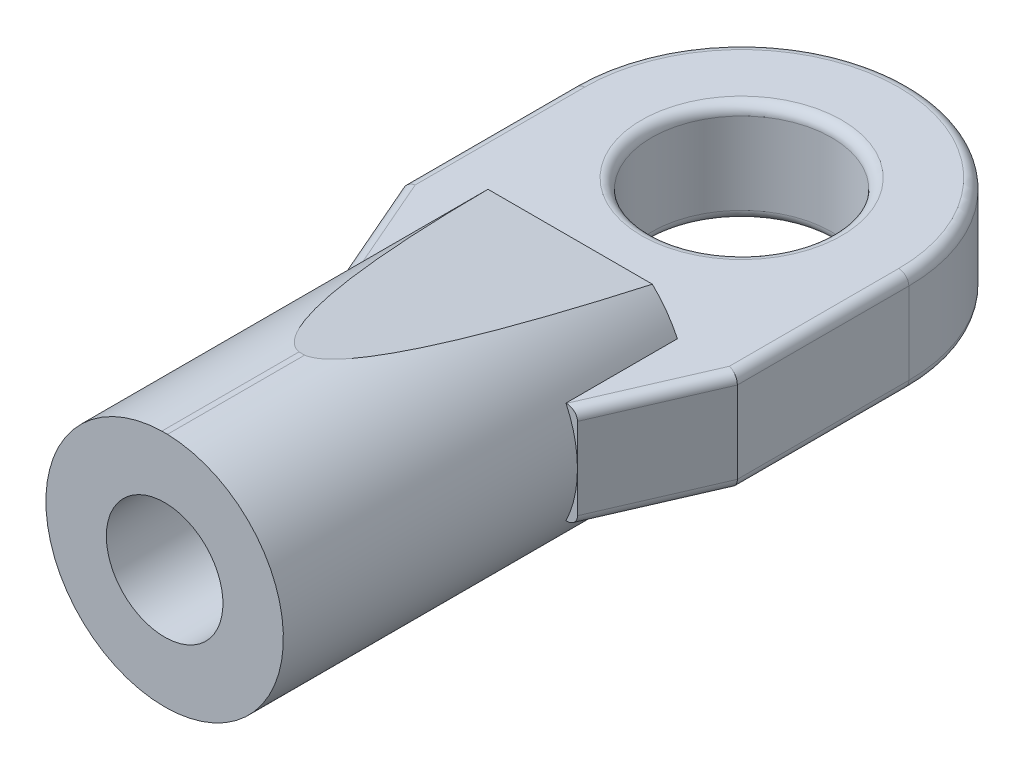
SolidWorks part; units mm, degrees
material "ABS"
ref_plane "Front Plane" through (0, 0, 0) normal (0, 0, 1) x (1, 0, 0)
ref_plane "Top Plane" through (0, 0, 0) normal (0, 1, 0) x (1, 0, 0)
ref_plane "Right Plane" through (0, 0, 0) normal (1, 0, 0) x (0, 0, -1)
sketch "Sketch1" plane through (0, 0, 0) normal (0, 1, 0) x (1, 0, 0)
  line L0 (0, -17.0942) -> (-1.7272, -17.0942)
  line L1 (0, 0) -> (0, -17.0942) construction
  line L2 (-3.5179, -17.0942) -> (-3.5179, -5.08)
  line L3 (-1.7272, -5.6642) -> (0, -5.6642)
  line L4 (-4.953, 0) -> (-4.953, -5.08)
  line L5 (4.953, 0) -> (4.953, -5.08)
  line L6 (-3.5179, -8.382) -> (-4.953, -5.08)
  line L7 (3.5179, -8.382) -> (4.953, -5.08)
  line L8 (-1.7272, -17.0942) -> (-1.7272, -5.6642)
  line L9 (-3.5179, -5.08) -> (0, -5.08)
  line L10 (-3.5179, -17.0942) -> (-1.7272, -17.0942)
  circle A0 centre (0, 0) radius 2.667
  arc A1 (4.953, 0) -> (-4.953, 0) centre (0, 0) ccw
  dimension "D1" = 2.286
  dimension "D7" = 1.7907
  dimension "D2" = 4.953
  dimension "D3" = 5.08
  dimension "D4" = 1.7272
  dimension "D5" = 3.6004
  dimension "D6" = 1.4351
  dimension "D8" = 11.43
  dimension "D9" = 12.0142
  dimension "D10" = 6.5674
revolve "Revolve1" add sketch "Sketch1" angle 360 about L1
sketch "Sketch2" plane through (0, 0, 0) normal (1, 0, 0) x (0, 0, -1)
  line L0 (-17.0942, -3.5189) -> (-17.0942, 3.5169)
  line L1 (-17.0942, -3.5189) -> (-13.0302, -3.5189)
  line L2 (-17.0942, 3.5169) -> (-13.0302, 3.5169)
  line L3 (-5.08, -2.541) -> (-5.08, 2.539)
  line L4 (-11.4553, 1.5113) -> (-11.4553, -1.5113)
  line L5 (-11.4553, -1.5113) -> (1.1177, -1.5113)
  line L6 (-11.4553, 1.5113) -> (1.1177, 1.5113)
  line L7 (-13.0302, 3.5169) -> (-5.08, 2.539)
  line L8 (-5.08, -2.541) -> (-13.0302, -3.5189)
  line L9 (-17.0942, 1.7262) -> (-5.6642, 1.7262)
  line L10 (-17.0942, -1.7282) -> (-5.6642, -1.7282)
  line L11 (-5.6642, -1.7282) -> (-5.6642, 1.7262)
  arc A0 (1.1177, -1.5113) -> (1.1177, 1.5113) centre (0, 0) ccw
  dimension "D1" = 3.4544
  dimension "D2" = 5.08
  dimension "D3" = 7.0358
  dimension "D4" = 4.064
  dimension "D5" = 7.9502
  dimension "D6" = 187.012
  dimension "D7" = 1.7907
  dimension "D8" = 0.5842
  dimension "D9" = 11.43
  dimension "D10" = 3.0226
  dimension "D11" = 17.0942
extrude "Cut-Extrude1" cut sketch "Sketch2" against normal up to surface and the other way up to surface flip side to cut contours L7 L3 L8 L1 L0 L2
sketch "Sketch7" plane through (0, 0, 0) normal (0, 1, 0) x (1, 0, 0)
  line L0 (0, 0) -> (0, -16.0633) construction
  line L1 (-4.953, 0) -> (-4.953, -5.08)
  line L2 (4.953, 0) -> (4.953, -5.08)
  line L3 (-3.5179, -8.382) -> (-4.953, -5.08)
  line L4 (3.5179, -8.382) -> (4.953, -5.08)
  line L5 (-3.5179, -8.382) -> (3.5179, -8.382)
  circle A0 centre (0, 0) radius 2.667
  arc A1 (4.953, 0) -> (-4.953, 0) centre (0, 0) ccw
  dimension "D4" = 5.334
  dimension "D5" = 4.953
  dimension "D6" = 4.953
  dimension "D7" = 2.286
  dimension "D1" = 5.08
  dimension "D2" = 3.6004
  dimension "D3" = 203.491
  dimension "D8" = 8.382
extrude "Boss-Extrude2" add sketch "Sketch7" along normal mid plane 3.02
fillet "Fillet1" radius 0.3 5 edges at (0, -1.51, -4.953) (-4.953, -1.51, 2.54) (-4.2354, -1.51, 6.731) (4.2355, -1.51, 6.731) (4.953, -1.51, 2.54)
fillet "Fillet2" radius 0.3 5 edges at (4.2355, 1.51, 6.731) (4.953, 1.51, 2.54) (0, 1.51, -4.953) (-4.953, 1.51, 2.54) (-4.2354, 1.51, 6.731)
fillet "Fillet3" radius 0.3 1 edges at (0, 1.51, 2.667)
fillet "Fillet4" radius 0.3 1 edges at (0, -1.51, 2.667)
sketch "Sketch8" plane through (0, 0, 0) normal (0, 0, 1) x (1, 0, 0)
  line L0 (0, 0) -> (0, 50000) construction
